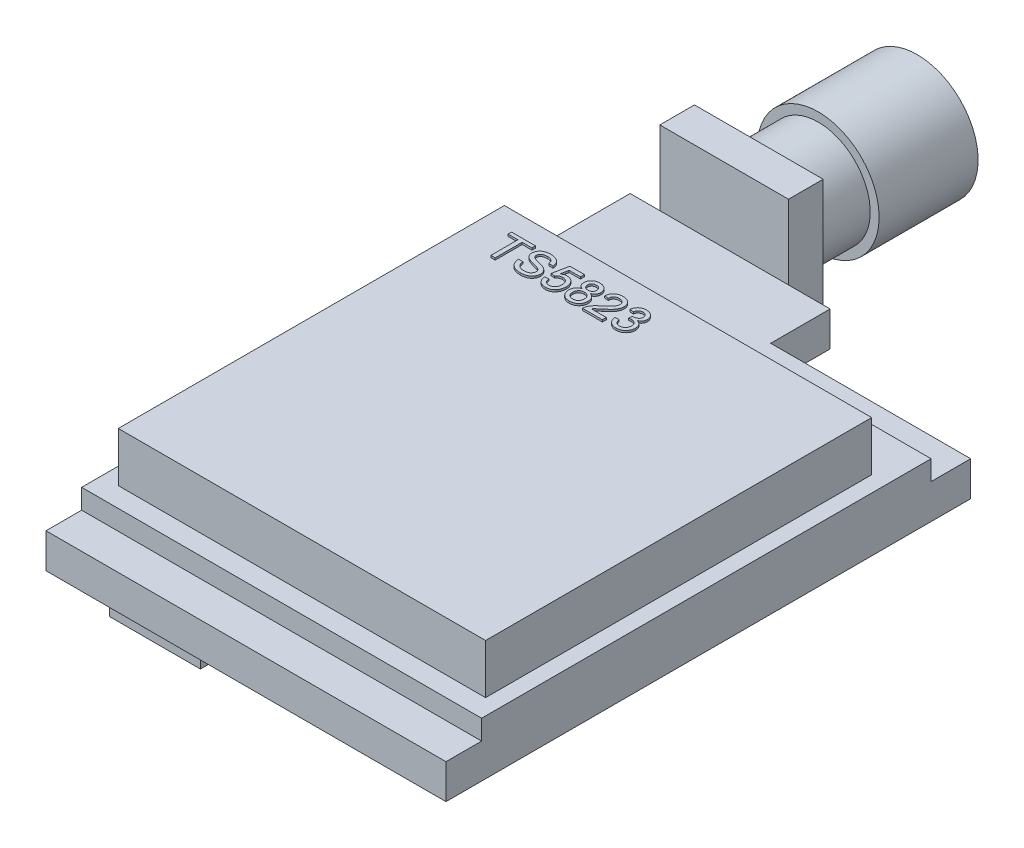
SolidWorks part; units mm, degrees
ref_plane "Спереди" through (0, 0, 0) normal (0, 0, 1) x (1, 0, 0)
ref_plane "Сверху" through (0, 0, 0) normal (0, 1, 0) x (1, 0, 0)
ref_plane "Справа" through (0, 0, 0) normal (1, 0, 0) x (0, 0, -1)
sketch "Эскиз1" plane through (0, 0, 0) normal (0, 1, 0) x (1, 0, 0)
  line L1 (10.1, -14.75) -> (-10.1, -14.75)
  line L2 (10.1, -14.75) -> (10.1, 14.75)
  line L3 (10.1, 14.75) -> (-10.1, 14.75)
  line L4 (-10.1, -14.75) -> (-10.1, 14.75)
  line L5 (10.1, -14.75) -> (-10.1, 14.75) construction
  line L6 (10.1, 14.75) -> (-10.1, -14.75) construction
  point P0 (0, 0)
  dimension "D1" = 29.5
  dimension "D2" = 20.2
extrude "main-pcb" add sketch "Эскиз1" along normal blind 1.75
sketch "Эскиз2" plane through (0, 1.75, 0) normal (0, 1, 0) x (1, 0, 0)
  line L0 (-10.1, 14.75) -> (-10.1, -14.75) construction
  line L1 (-10.1, 9.75) -> (10.1, 9.75)
  line L2 (-10.1, 9.75) -> (-10.1, -12.95)
  line L3 (-10.1, -12.95) -> (10.1, -12.95)
  line L4 (10.1, 9.75) -> (10.1, -12.95)
  line L5 (10.1, -14.75) -> (10.1, 14.75) construction
  line L6 (-10.1, -14.75) -> (10.1, -14.75) construction
  line L7 (10.1, 14.75) -> (-10.1, 14.75) construction
  dimension "D1" = 1.8
  dimension "D2" = 5
extrude "radio-module-pcb" add sketch "Эскиз2" along normal blind 1
sketch "Эскиз3" plane through (0, 2.75, 0) normal (0, 1, 0) x (1, 0, 0)
  line L0 (-10.1, -12.95) -> (10.1, -12.95) construction
  line L1 (-9.25, 7.55) -> (9.3, 7.55)
  line L2 (-9.25, 7.55) -> (-9.25, -11.95)
  line L3 (-9.25, -11.95) -> (9.3, -11.95)
  line L4 (9.3, 7.55) -> (9.3, -11.95)
  line L5 (10.1, -12.95) -> (10.1, 9.75) construction
  dimension "D1" = 19.5
  dimension "D2" = 18.55
  dimension "D3" = 1
  dimension "D4" = 0.8
extrude "radio-module" add sketch "Эскиз3" along normal blind 2.5
sketch "Эскиз4" plane through (0, 0, -14.75) normal (0, 0, -1) x (-1, 0, 0)
  line L0 (10.1, 1.75) -> (10.1, 0) construction
  line L1 (8.6, -1) -> (2.1, -1)
  line L2 (8.6, -1) -> (8.6, 5.5)
  line L3 (8.6, 5.5) -> (2.1, 5.5)
  line L4 (2.1, -1) -> (2.1, 5.5)
  line L5 (-10.1, 0) -> (10.1, 0) construction
  dimension "D1" = 1.5
  dimension "D2" = 6.5
  dimension "D3" = 6.5
  dimension "D4" = 1
extrude "antenna-socket" add sketch "Эскиз4" along normal blind 1.75
sketch "Эскиз5" plane through (0, 0, -16.5) normal (0, 0, -1) x (-1, 0, 0)
  line L0 (2.1, 2.25) -> (8.6, 2.25) construction
  line L1 (2.1, 5.5) -> (2.1, -1) construction
  line L2 (8.6, -1) -> (8.6, 5.5) construction
  circle A0 centre (5.35, 2.25) radius 2.625
  dimension "D1" = 5.25
extrude "antenna-ring" add sketch "Эскиз5" along normal blind 3
sketch "Эскиз6" plane through (0, 0, -19.5) normal (0, 0, -1) x (-1, 0, 0)
  circle A0 centre (5.35, 2.25) radius 3.075
  dimension "D1" = 6.15
extrude "antenna-nut" add sketch "Эскиз6" along normal blind 5
sketch "Эскиз7" plane through (0, 0, -24.5) normal (0, 0, -1) x (-1, 0, 0)
  circle A0 centre (5.35, 2.25) radius 0.5
  circle A1 centre (5.35, 2.25) radius 2.075
  circle A2 centre (5.35, 2.25) radius 3.075 construction
  dimension "D1" = 1
  dimension "D2" = 1
extrude "antenna-connector" cut sketch "Эскиз7" against normal blind 2
sketch "Эскиз9" plane through (0, 0, 0) normal (0, -1, 0) x (1, 0, 0)
  line L1 (-2.1, -14.75) -> (-3.1, -14.75)
  line L2 (-2.1, -14.75) -> (-2.1, -10.75)
  line L3 (-2.1, -10.75) -> (-3.1, -10.75)
  line L4 (-3.1, -14.75) -> (-3.1, -10.75)
  line L5 (-8.6, -14.75) -> (-7.6, -14.75)
  line L6 (-8.6, -14.75) -> (-8.6, -10.75)
  line L7 (-8.6, -10.75) -> (-7.6, -10.75)
  line L8 (-7.6, -14.75) -> (-7.6, -10.75)
  dimension "D1" = 4
  dimension "D2" = 1
  dimension "D3" = 4
  dimension "D4" = 1
extrude "antenna-leg" add sketch "Эскиз9" along normal up to surface (1 mm away) up to face at (-5.35, -1, -15.625)
sketch "Эскиз17" plane through (0, 5.25, 0) normal (0, 1, 0) x (1, 0, 0)
  text T0 "TS5823" font "Arial" height in points 6
extrude "NAME-TS5823" add sketch "Эскиз17" along normal blind 0.1
sketch "Эскиз18" plane through (0, 0, 0) normal (0, -1, 0) x (1, 0, 0)
  line L0 (-10.1, -14.75) -> (-10.1, 14.75) construction
  line L1 (10.1, -14.75) -> (0, -14.75)
  line L2 (10.1, -14.75) -> (10.1, -11.75)
  line L3 (10.1, -11.75) -> (0, -11.75)
  line L4 (0, -14.75) -> (0, -11.75)
  dimension "D1" = 10.1
  dimension "D2" = 3
extrude "pcb-cut-out" cut sketch "Эскиз18" against normal through all
sketch "Эскиз19" plane through (0, 0, 0) normal (0, -1, 0) x (1, 0, 0)
  line L0 (-10.1, -14.75) -> (-10.1, 14.75) construction
  line L1 (-2.2, -7.55) -> (-7.7, -7.55)
  line L2 (-2.2, -7.55) -> (-2.2, 1.85)
  line L3 (-2.2, 1.85) -> (-7.7, 1.85)
  line L4 (-7.7, -7.55) -> (-7.7, 1.85)
  line L5 (-8.6, -14.75) -> (-10.1, -14.75) construction
  dimension "D1" = 5.5
  dimension "D2" = 9.4
  dimension "D3" = 2.4
  dimension "D4" = 7.2
extrude "Бобышка-Вытянуть1" add sketch "Эскиз19" along normal blind 2.5
sketch "Эскиз21" plane through (0, -2.5, 0) normal (0, -1, 0) x (1, 0, 0)
  line L0 (-4.95, -7.55) -> (-4.95, 1.85) construction
  line L1 (-7.7, -7.55) -> (-2.2, -7.55) construction
  line L2 (-2.2, 1.85) -> (-7.7, 1.85) construction
  line L4 (-3.95, -7.1261) -> (-5.95, -7.1261)
  line L5 (-3.95, -7.1261) -> (-3.95, -6.3261)
  line L6 (-3.95, -6.3261) -> (-5.95, -6.3261)
  line L7 (-5.95, -7.1261) -> (-5.95, -6.3261)
  line L8 (-3.95, -7.1261) -> (-5.95, -6.3261) construction
  line L9 (-3.95, -6.3261) -> (-5.95, -7.1261) construction
  point P6 (-4.95, -6.7261)
  dimension "D1" = 0.8
  dimension "D2" = 2
extrude "jimpes-switch" cut sketch "Эскиз21" against normal blind 0.4
pattern_linear "Линейный массив1" count 6 spacing 1.5 along (0, 0, 1) of "jimpes-switch"
sketch "Эскиз22" plane through (0, 0, 0) normal (0, -1, 0) x (1, 0, 0)
  line L0 (-10.1, -14.75) -> (-10.1, 14.75) construction
  line L1 (-9.5, 12.15) -> (-4.9, 12.15)
  line L2 (-9.5, 12.15) -> (-9.5, 4.95)
  line L3 (-9.5, 4.95) -> (-4.9, 4.95)
  line L4 (-4.9, 12.15) -> (-4.9, 4.95)
  line L5 (-10.1, 14.75) -> (10.1, 14.75) construction
  dimension "D1" = 7.2
  dimension "D2" = 4.6
  dimension "D3" = 0.6
  dimension "D4" = 2.6
extrude "Бобышка-Вытянуть2" add sketch "Эскиз22" along normal blind 3
sketch "Эскиз23" plane through (-9.5, 0, 0) normal (-1, 0, 0) x (0, 0, 1)
  line L0 (4.95, -1.5) -> (12.15, -1.5) construction
  line L1 (4.95, -3) -> (4.95, 0) construction
  line L2 (12.15, -3) -> (12.15, 0) construction
  line L3 (12.15, -3) -> (4.95, -3) construction
  line L4 (11.65, -0.5) -> (5.45, -0.5)
  line L5 (11.65, -0.5) -> (11.65, -2.5)
  line L6 (11.65, -2.5) -> (5.45, -2.5)
  line L7 (5.45, -0.5) -> (5.45, -2.5)
  line L8 (11.65, -0.5) -> (5.45, -2.5) construction
  line L9 (11.65, -2.5) -> (5.45, -0.5) construction
  point P6 (8.55, -1.5)
  dimension "D1" = 0.5
  dimension "D2" = 0.5
extrude "Вырез-Вытянуть4" cut sketch "Эскиз23" against normal blind 4
sketch "Эскиз24" plane through (-5.5, 0, 0) normal (-1, 0, 0) x (0, 0, 1)
  line L0 (5.45, -1.8) -> (11.65, -1.8) construction
  line L1 (5.45, -0.5) -> (5.45, -2.5) construction
  line L2 (11.65, -2.5) -> (11.65, -0.5) construction
  line L3 (12.15, -3) -> (4.95, -3) construction
  line L4 (8.75, -1.5) -> (8.35, -1.5)
  line L5 (8.75, -1.5) -> (8.75, -2.1)
  line L6 (8.75, -2.1) -> (8.35, -2.1)
  line L7 (8.35, -1.5) -> (8.35, -2.1)
  line L8 (8.75, -1.5) -> (8.35, -2.1) construction
  line L9 (8.75, -2.1) -> (8.35, -1.5) construction
  point P6 (8.55, -1.8)
  dimension "D1" = 1.2
  dimension "D2" = 0.6
  dimension "D3" = 0.4
extrude "Бобышка-Вытянуть3" add sketch "Эскиз24" along normal blind 3
pattern_linear "Линейный массив2" count 3 spacing 1 along (0, 0, 1) count 3 spacing 1 along (0, 0, -1) of "Бобышка-Вытянуть3"
